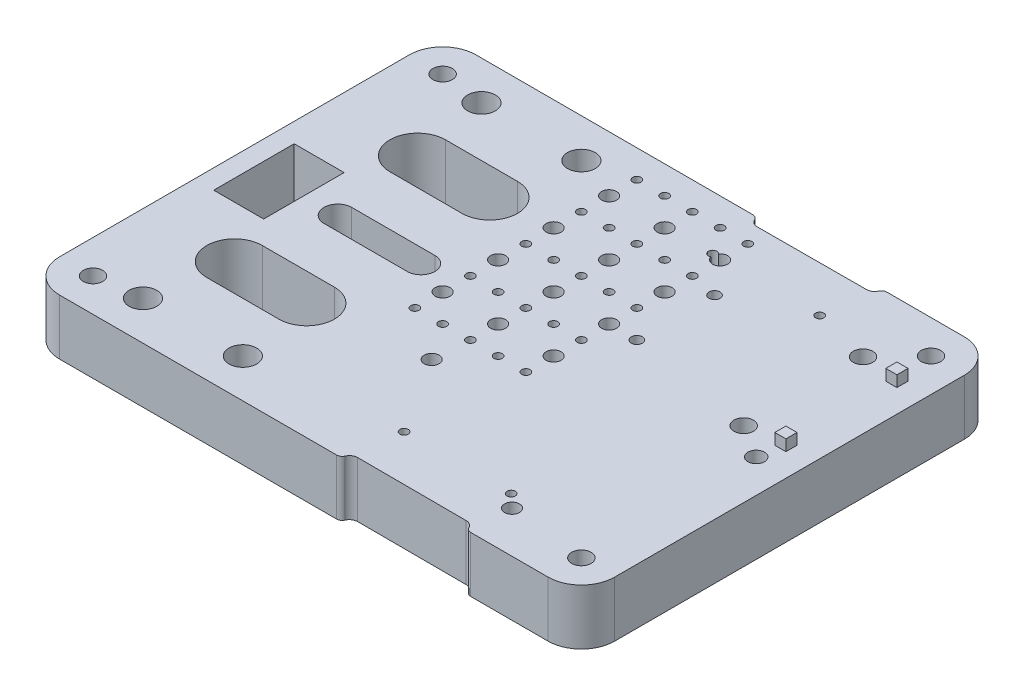
SolidWorks part; units mm, degrees
ref_plane "Спереди" through (0, 0, 0) normal (0, 0, 1) x (1, 0, 0)
ref_plane "Сверху" through (0, 0, 0) normal (0, 1, 0) x (1, 0, 0)
ref_plane "Справа" through (0, 0, 0) normal (1, 0, 0) x (0, 0, -1)
sketch "Эскиз1" plane through (0, 0, 0) normal (0, 1, 0) x (1, 0, 0)
  line L0 (0, 37.5) -> (100, 37.5) construction
  line L17 (0, 0) -> (100, 0)
  line L18 (0, 0) -> (0, 75)
  line L19 (0, 75) -> (100, 75)
  line L20 (100, 0) -> (100, 75)
  line L21 (50, 75) -> (50, 0) construction
  line L22 (23, 75) -> (23, 0) construction
  line L25 (16.5, 54) -> (29.5, 54) construction
  line L26 (16.5, 59) -> (29.5, 59)
  line L27 (16.5, 49) -> (29.5, 49)
  line L28 (16.5, 21) -> (29.5, 21) construction
  line L29 (16.5, 16) -> (29.5, 16)
  line L30 (16.5, 26) -> (29.5, 26)
  line L31 (68, 75) -> (68, 0) construction
  line L33 (3.5, 44.75) -> (12.5, 44.75)
  line L34 (3.5, 44.75) -> (3.5, 30.25)
  line L35 (3.5, 30.25) -> (12.5, 30.25)
  line L36 (12.5, 44.75) -> (12.5, 30.25)
  line L37 (3.5, 44.75) -> (12.5, 30.25) construction
  line L38 (3.5, 30.25) -> (12.5, 44.75) construction
  circle A8 centre (6, 69) radius 1.75
  circle A9 centre (94, 69) radius 1.75
  circle A10 centre (94, 6) radius 1.75
  circle A11 centre (6, 6) radius 1.75
  circle A16 centre (14, 68) radius 1.25
  circle A17 centre (32, 68) radius 1.25
  arc A18 (16.5, 59) -> (16.5, 49) centre (16.5, 54) ccw
  arc A19 (29.5, 49) -> (29.5, 59) centre (29.5, 54) ccw
  arc A20 (16.5, 16) -> (16.5, 26) centre (16.5, 21) cw
  arc A21 (29.5, 26) -> (29.5, 16) centre (29.5, 21) cw
  circle A22 centre (32, 7) radius 1.25
  circle A23 centre (14, 7) radius 1.25
  circle A24 centre (58.35, 65.3) radius 0.75
  circle A25 centre (77.65, 65.3) radius 0.75
  circle A26 centre (77.65, 9.7) radius 0.75
  circle A27 centre (58.35, 9.7) radius 0.75
  circle A28 centre (94, 37.5) radius 1.5
  point P13 (23, 54)
  point P23 (23, 21)
  point P51 (8, 37.5)
  dimension "D3" = 18
  dimension "D8" = 21
  dimension "D9" = 2.5
  dimension "D10" = 1.5
  dimension "D12" = 55.6
  dimension "D15" = 3.5
  dimension "D4" = 23
  dimension "D11" = 19.3
  dimension "D20" = 3
  dimension "D1" = 75
  dimension "D2" = 100
  dimension "D5" = 7
  dimension "D6" = 10
  dimension "D7" = 13
  dimension "D13" = 6
  dimension "D14" = 6
  dimension "D16" = 32
  dimension "D17" = 9
  dimension "D18" = 14.5
  dimension "D19" = 8
  dimension "D21" = 6
extrude "Бобышка-Вытянуть1" add sketch "Эскиз1" along normal blind 10
fillet "Скругление5" radius 6 4 edges at (100, 5, 0) (100, 5, -75) (0, 5, 0) (0, 5, -75)
sketch "Эскиз2" plane through (0, 0, 0) normal (0, -1, 0) x (1, 0, 0)
  line L0 (18.6125, -37.5) -> (33.6125, -37.5) construction
  line L1 (100, -6) -> (100, -69) construction
  line L2 (100, -52) -> (4.002, -52) construction
  line L3 (94, -75) -> (6, -75) construction
  line L4 (18.6125, -35) -> (33.6125, -35)
  line L5 (18.6125, -40) -> (33.6125, -40)
  line L6 (12.5, -30.25) -> (12.5, -44.75) construction
  circle A3 centre (80, -7.5) radius 1.35
  circle A35 centre (88, -62.75) radius 1.75
  circle A36 centre (88, -41.25) radius 1.75
  arc A37 (18.6125, -35) -> (18.6125, -40) centre (18.6125, -37.5) ccw
  arc A38 (33.6125, -40) -> (33.6125, -35) centre (33.6125, -37.5) ccw
  circle A68 centre (49.5509, -23.4735) radius 1.35
  circle A70 centre (49.5509, -7.5) radius 1.35 [skipped]
  circle A71 centre (80, -23.4735) radius 1.35 [skipped]
  circle A72 centre (65, -59) radius 1
  circle A73 centre (65, -45) radius 1
  point P20 (26.1125, -37.5)
  point P25 (0, 0)
  point P26 (12.5, -37.5)
  point P27 (49.5509, -37.5)
  dimension "D1" = 2
  dimension "D5" = 2
  dimension "D7" = 3.5
  dimension "D12" = 2.7
  dimension "D4" = 35
  dimension "D3" = 14
  dimension "D6" = 23
  dimension "D8" = 21.5
  dimension "D9" = 12
  dimension "D10" = 5
  dimension "D11" = 15
  dimension "D2" = 2
extrude "Вырез-Вытянуть1" cut sketch "Эскиз2" against normal up to next
sketch "Эскиз3" plane through (0, 10, 0) normal (0, 1, 0) x (1, 0, 0)
  circle A0 centre (14, 68) radius 2.5
  circle A1 centre (32, 68) radius 2.5
  circle A2 centre (14, 7) radius 2.5
  circle A3 centre (32, 7) radius 2.5
  dimension "D1" = 5
extrude "Вырез-Вытянуть2" cut sketch "Эскиз3" against normal blind 7
sketch "Эскиз4" plane through (0, 10, 0) normal (0, 1, 0) x (1, 0, 0)
  line L0 (100, 52) -> (0, 52) construction
  line L1 (100, 6) -> (100, 69) construction
  line L2 (0, 69) -> (0, 6) construction
  line L3 (94, 75) -> (6, 75) construction
  line L5 (93.8557, 43) -> (95.8557, 43)
  line L6 (93.8557, 43) -> (93.8557, 41)
  line L7 (93.8557, 41) -> (95.8557, 41)
  line L8 (95.8557, 43) -> (95.8557, 41)
  line L9 (93.8557, 63) -> (95.8557, 63)
  line L10 (93.8557, 63) -> (93.8557, 61)
  line L11 (93.8557, 61) -> (95.8557, 61)
  line L12 (95.8557, 63) -> (95.8557, 61)
  dimension "D1" = 23
  dimension "D2" = 2
  dimension "D3" = 18
extrude "Бобышка-Вытянуть2" add sketch "Эскиз4" along normal blind 2
sketch "Эскиз5" plane through (0, 10, 0) normal (0, 1, 0) x (1, 0, 0)
  line L0 (58.2, 0) -> (77.8, -0.0607) construction
  line L1 (6, 0) -> (94, 0) construction
  line L2 (58.2046, 1.5) -> (77.8046, 1.4393)
  line L3 (58.1954, -1.5) -> (77.7954, -1.5607)
  line L4 (0, 37.5) -> (100, 37.5) construction
  line L5 (0, 69) -> (0, 6) construction
  line L6 (100, 6) -> (100, 69) construction
  line L7 (58.2, 75) -> (77.8, 75.0607) construction
  line L8 (58.2046, 73.5) -> (77.8046, 73.5607)
  line L9 (58.1954, 76.5) -> (77.7954, 76.5607)
  arc A0 (58.2046, 1.5) -> (58.1954, -1.5) centre (58.2, 0) ccw
  arc A1 (77.7954, -1.5607) -> (77.8046, 1.4393) centre (77.8, -0.0607) ccw
  arc A2 (58.2046, 73.5) -> (58.1954, 76.5) centre (58.2, 75) cw
  arc A3 (77.7954, 76.5607) -> (77.8046, 73.5607) centre (77.8, 75.0607) cw
  point P4 (68, -0.0303)
  point P17 (68, 75.0303)
  dimension "D1" = 3
  dimension "D2" = 19.6001
extrude "Вырез-Вытянуть3" cut sketch "Эскиз5" against normal blind 36.8
fillet "Скругление6" radius 1 4 edges at (56.7, 5, -75) (79.2988, 5, -75) (79.2988, 5, 0) (56.7, 5, 0)
sketch "Эскиз6" plane through (0, 10, 0) normal (0, 1, 0) x (1, 0, 0)
  line L0 (55.9087, 75) -> (6, 75) construction
  line L1 (0, 69) -> (0, 6) construction
  circle A0 centre (40, 65) radius 1.35
  circle A1 centre (50, 65) radius 1.35
  circle A2 centre (60, 65) radius 1.35
  circle A3 centre (50, 55) radius 1.35
  circle A4 centre (60, 55) radius 1.35
  circle A5 centre (50, 45) radius 1.35
  circle A6 centre (60, 45) radius 1.35
  circle A7 centre (50, 35) radius 1.35
  circle A8 centre (60, 35) radius 1.35
  circle A9 centre (40, 55) radius 1.35
  circle A10 centre (40, 45) radius 1.35
  circle A11 centre (40, 35) radius 1.35
  circle A12 centre (40, 70) radius 0.75
  circle A13 centre (45, 70) radius 0.75
  circle A14 centre (50, 70) radius 0.75
  circle A15 centre (55, 70) radius 0.75
  circle A16 centre (60, 70) radius 0.75
  circle A17 centre (45, 60) radius 0.75
  circle A18 centre (50, 60) radius 0.75
  circle A19 centre (55, 60) radius 0.75
  circle A20 centre (60, 60) radius 0.75
  circle A21 centre (45, 50) radius 0.75
  circle A22 centre (50, 50) radius 0.75
  circle A23 centre (55, 50) radius 0.75
  circle A24 centre (60, 50) radius 0.75
  circle A25 centre (45, 40) radius 0.75
  circle A26 centre (50, 40) radius 0.75
  circle A27 centre (55, 40) radius 0.75
  circle A28 centre (60, 40) radius 0.75
  circle A29 centre (45, 30) radius 0.75
  circle A30 centre (50, 30) radius 0.75
  circle A31 centre (55, 30) radius 0.75
  circle A32 centre (60, 30) radius 0.75
  circle A33 centre (40, 60) radius 0.75
  circle A34 centre (40, 50) radius 0.75
  circle A35 centre (40, 40) radius 0.75
  circle A36 centre (40, 30) radius 0.75
  dimension "D1" = 2.7
  dimension "D8" = 1.5
  dimension "D4" = 10
  dimension "D5" = 40
  dimension "D6" = 10
  dimension "D7" = 10
  dimension "D9" = 5
  dimension "D2" = 3
  dimension "D3" = 4
  dimension "D10" = 5
  dimension "D11" = 5
extrude "Вырез-Вытянуть4" cut sketch "Эскиз6" against normal blind 36.8
